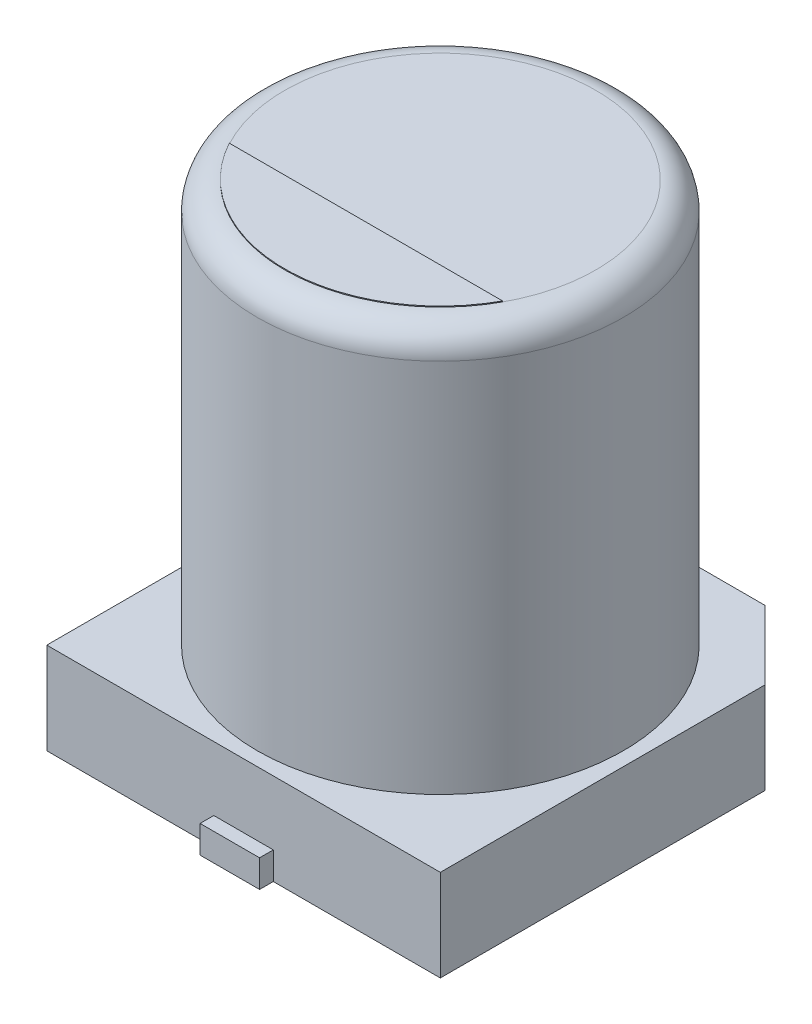
SolidWorks part; units mm, degrees
ref_plane "Front Plane" through (0, 0, 0) normal (0, 0, 1) x (1, 0, 0)
ref_plane "Top Plane" through (0, 0, 0) normal (0, 1, 0) x (1, 0, 0)
ref_plane "Right Plane" through (0, 0, 0) normal (1, 0, 0) x (0, 0, -1)
sketch "Sketch2" plane through (0, 0, 0) normal (0, 1, 0) x (1, 0, 0)
  line L0 (0, 0) -> (0, 2.085) construction
  line L1 (0, 0) -> (2.9643, 0) construction
  line L2 (2.15, -2.15) -> (-2.15, -2.15)
  line L3 (-2.15, -2.15) -> (-2.15, 1.4)
  line L4 (-2.15, 1.4) -> (-1.4, 2.15)
  line L5 (-1.4, 2.15) -> (1.4, 2.15)
  line L6 (1.4, 2.15) -> (2.15, 1.4)
  line L7 (2.15, 1.4) -> (2.15, -2.15)
  line L8 (0, -2.15) -> (0, -0.9795) construction
  line L9 (0, 2.15) -> (0, 2.1922) construction
  line L10 (-0.2934, -2.15) -> (-0.2934, 2.15) construction
  line L11 (-0.2934, 0) -> (-0.8682, 0) construction
  dimension "D1" = 4.3
  dimension "D2" = 4.3
  dimension "D3" = 2.8
extrude "Boss-Extrude1" add sketch "Sketch2" along normal blind 1
sketch "Sketch3" plane through (0, 0, 0) normal (0, 1, 0) x (1, 0, 0)
  circle A0 centre (0, 0) radius 2
  dimension "D1" = 4
extrude "Boss-Extrude2" add sketch "Sketch3" along normal blind 5.4 contours A0
fillet "Fillet1" radius 0.3 1 edges at (0, 5.4, 2)
sketch "Sketch4" plane through (0, 0, 0) normal (0, 1, 0) x (1, 0, 0)
  line L13 (0, 0) -> (0.2882, 0) construction
  line L14 (0.325, 2.3) -> (-0.325, 2.3)
  line L15 (0.325, -0.5) -> (-0.325, -0.5)
  line L16 (0.325, -0.5) -> (0.325, -2.3)
  line L17 (0.325, -2.3) -> (-0.325, -2.3)
  line L18 (-0.325, -0.5) -> (-0.325, -2.3)
  line L19 (0.325, -0.5) -> (-0.325, -2.3) construction
  line L20 (0.325, -2.3) -> (-0.325, -0.5) construction
  line L21 (-0.325, 0.5) -> (-0.325, 2.3)
  line L22 (0.325, 0.5) -> (-0.325, 0.5)
  line L23 (0.325, 0.5) -> (0.325, 2.3)
  line L24 (0.325, 2.3) -> (-0.325, 0.5) construction
  line L25 (0.325, 0.5) -> (-0.325, 2.3) construction
  point P14 (0, -1.4)
  point P24 (0, 1.4)
  dimension "D4" = 0.65
  dimension "D5" = 1.8
  dimension "D6" = 1
extrude "Boss-Extrude3" add sketch "Sketch4" along normal blind 0.3
ref_plane "Plane1" through (0, 5.4, 0) normal (0, 1, 0) x (1, 0, 0)
sketch "Sketch5" plane through (0, 5.4, 0) normal (0, 1, 0) x (1, 0, 0)
  line L0 (1.493, -0.8129) -> (-1.493, -0.8129)
  circle A0 centre (0, 0) radius 1.7 construction
  arc A1 (1.493, -0.8129) -> (-1.493, -0.8129) centre (0, 0) cw
extrude "Boss-Extrude4" add sketch "Sketch5" along normal blind 0.01
